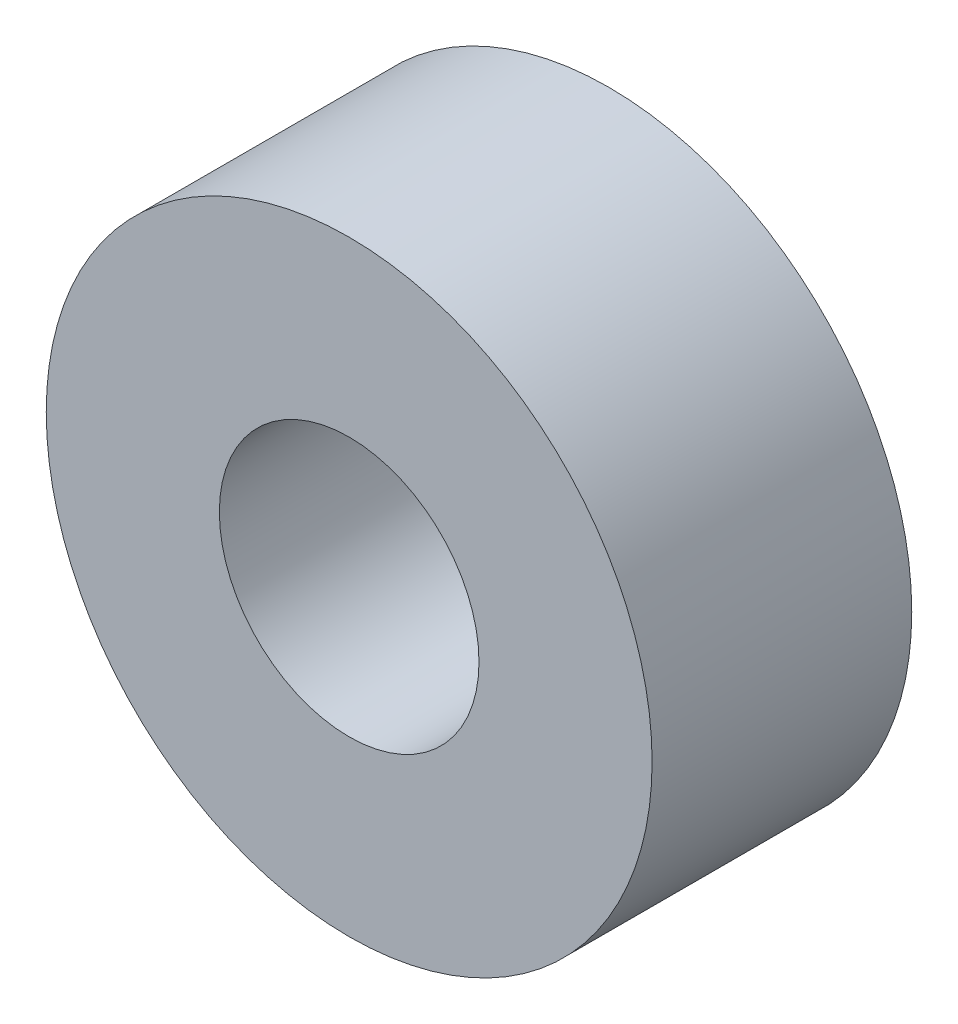
SolidWorks part; units mm, degrees
ref_plane "Front Plane" through (0, 0, 0) normal (0, 0, 1) x (1, 0, 0)
ref_plane "Top Plane" through (0, 0, 0) normal (0, 1, 0) x (1, 0, 0)
ref_plane "Right Plane" through (0, 0, 0) normal (1, 0, 0) x (0, 0, -1)
sketch "Sketch1" plane through (0, 0, 0) normal (0, 0, 1) x (1, 0, 0)
  circle A0 centre (0, 0) radius 3.5
  circle A1 centre (0, 0) radius 1.5
  dimension "D1" = 3
  dimension "D2" = 7
extrude "Boss-Extrude1" add sketch "Sketch1" along normal mid plane 3
